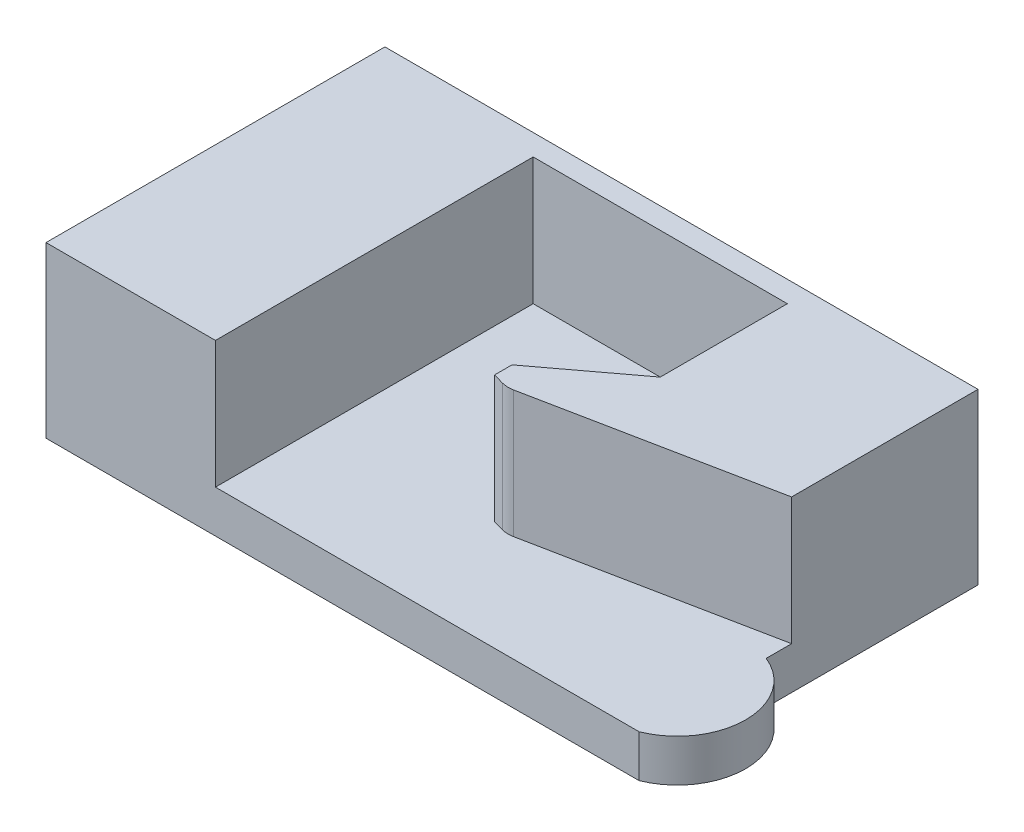
SolidWorks part; units mm, degrees
ref_plane "Front Plane" through (0, 0, 0) normal (0, 0, 1) x (1, 0, 0)
ref_plane "Top Plane" through (0, 0, 0) normal (0, 1, 0) x (1, 0, 0)
ref_plane "Right Plane" through (0, 0, 0) normal (1, 0, 0) x (0, 0, -1)
sketch "Sketch1" plane through (0, 0, 0) normal (0, 1, 0) x (1, 0, 0)
  line L0 (0, 0) -> (70, 0)
  line L1 (0, 0) -> (0, 40)
  line L2 (70, 0) -> (70, 40)
  line L3 (0, 40) -> (70, 40)
  dimension "D1" = 70
  dimension "D2" = 40
extrude "Boss-Extrude1" add sketch "Sketch1" along normal blind 20
sketch "Sketch2" plane through (0, 20, 0) normal (0, 1, 0) x (1, 0, 0)
  line L0 (20, 15) -> (20, 37.5)
  line L1 (20, 37.5) -> (50, 37.5)
  line L2 (50, 37.5) -> (50, 22.5)
  line L3 (40, 15) -> (20, 15)
  line L4 (50, 22.5) -> (40, 15)
  line L5 (70, 40) -> (0, 40) construction
  line L6 (0, 40) -> (0, 0) construction
  dimension "D1" = 2.5
  dimension "D2" = 25
  dimension "D3" = 20
  dimension "D4" = 20
  dimension "D5" = 30
  dimension "D6" = 15
extrude "Cut-Extrude1" cut sketch "Sketch2" against normal blind 15
sketch "Sketch3" plane through (0, 20, 0) normal (0, 1, 0) x (1, 0, 0)
  line L0 (40, 15) -> (40, 0)
  line L1 (40, 15) -> (20, 15)
  line L2 (40, 0) -> (20, 0)
  line L3 (20, 15) -> (20, 0)
  line L4 (0, 0) -> (70, 0) construction
  line L6 (20, 37.5) -> (20, 15) construction
extrude "Cut-Extrude2" cut sketch "Sketch3" against normal up to surface (15 mm away) up to face at (36, 5, -25.5)
sketch "Sketch4" plane through (0, 20, 0) normal (0, 1, 0) x (1, 0, 0)
  line L0 (40, 12) -> (70, 18)
  line L1 (70, 0) -> (70, 40) construction
  line L2 (70, 18) -> (70, 0)
  line L3 (70, 0) -> (40, 0)
  line L4 (40, 0) -> (40, 12)
  line L5 (40, 0) -> (40, 15) construction
  dimension "D1" = 18
  dimension "D2" = 3
extrude "Cut-Extrude3" cut sketch "Sketch4" against normal up to surface (15 mm away) up to face at (36.6667, 5, -18.75)
chamfer "Chamfer1" distance 2 angle 27 1 edges at (40, 12.5, -12)
fillet "Fillet1" radius 3 1 edges at (41.9612, 12.5, -12.3922)
sketch "Sketch5" plane through (0, 0, 0) normal (0, -1, 0) x (1, 0, 0)
  line L0 (70, 0) -> (70, -40) construction
  line L1 (70, -15) -> (70, 0)
  arc A0 (70, 0) -> (70, -15) centre (67, -7.5) cw
  dimension "D1" = 15
  dimension "D2" = 3
extrude "Boss-Extrude2" add sketch "Sketch5" against normal up to surface (5 mm away) up to face at (44.3932, 5, -16.8481)
